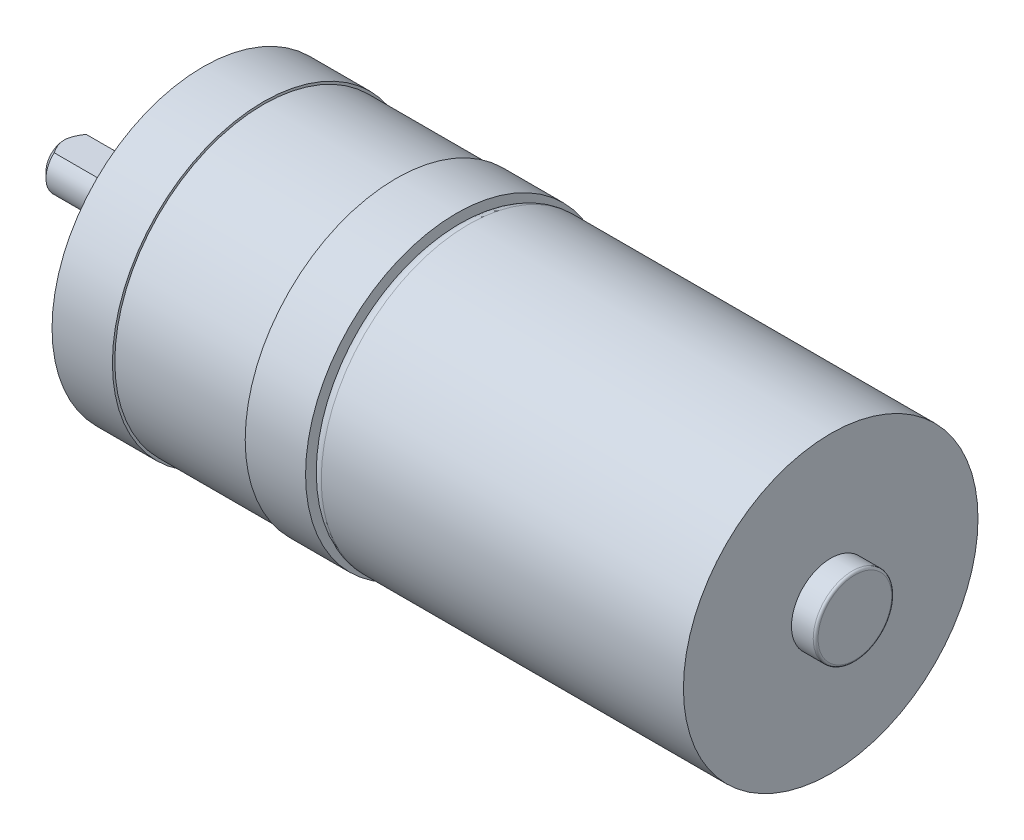
SolidWorks part; units mm, degrees
ref_plane "Front Plane" through (0, 0, 0) normal (0, 0, 1) x (1, 0, 0)
ref_plane "Top Plane" through (0, 0, 0) normal (0, 1, 0) x (1, 0, 0)
ref_plane "Right Plane" through (0, 0, 0) normal (1, 0, 0) x (0, 0, -1)
sketch "Sketch1" plane through (0, 0, 0) normal (0, 0, 1) x (1, 0, 0)
  line L0 (-23.0064, 0) -> (42.0533, 0) construction
  line L1 (-9.9467, -3.5317) -> (-9.9467, -12.5)
  line L2 (-12.4467, -2) -> (-12.4467, -3.5317)
  line L3 (-12.4467, -3.5317) -> (-9.9467, -3.5317)
  line L4 (-21.4467, 0) -> (-21.4467, -1.5)
  line L5 (-12.4467, 0) -> (-12.4467, -12.5) construction
  line L6 (-20.9467, -2) -> (-12.4467, -2)
  line L7 (-23.0064, -2) -> (27.3668, -2) construction
  line L8 (-21.4467, 0) -> (-21.4467, -12.5) construction
  line L9 (-9.9467, 0) -> (-9.9467, -12.5) construction
  line L10 (-21.4467, 0) -> (44.0533, 0)
  line L11 (11.0533, -11.2) -> (11.0533, -12.5)
  line L12 (-9.9467, -12.5) -> (-4.9467, -12.5)
  line L13 (11.0533, -3.5317) -> (11.0533, -12.5) construction
  line L14 (12.0533, -12.2) -> (42.0533, -12.2)
  line L15 (42.0533, -12.2) -> (42.0533, -3.25)
  line L16 (-23.0064, 0) -> (27.3668, 0) construction
  line L17 (-21.4467, -1.5) -> (-20.9467, -2)
  line L18 (-4.9467, -12.3) -> (-4.9467, -12.5)
  line L19 (6.0533, -12.3) -> (6.0533, -12.5)
  line L20 (-4.9467, -12.3) -> (6.0533, -12.3)
  line L21 (-4.9467, -3.5317) -> (-4.9467, -12.5) construction
  line L22 (-9.9467, -12.3) -> (11.0533, -12.3) construction
  line L23 (6.0533, -12.5) -> (11.0533, -12.5)
  line L24 (-9.9467, -12.5) -> (11.0533, -12.5) construction
  line L25 (6.0533, -12.2) -> (6.0533, -12.5) construction
  line L26 (44.0533, -3.05) -> (44.0533, 0)
  line L28 (44.0533, -12.2) -> (44.0533, 0) construction
  line L29 (42.0533, -12.2) -> (42.0533, 0) construction
  line L30 (42.0533, -3.25) -> (43.8533, -3.25)
  line L31 (11.0533, -12.2) -> (11.0533, -12.5) construction
  arc A0 (43.8533, -3.25) -> (44.0533, -3.05) centre (43.8533, -3.05) ccw
  arc A1 (12.0533, -12.2) -> (11.0533, -11.2) centre (12.0533, -11.2) cw
  point P13 (-21.4467, -2)
  dimension "D8" = 0.2
  dimension "D6" = 1
  dimension "D1" = 5
  dimension "D10" = 12.2
  dimension "D11" = 1.8
  dimension "D2" = 2.5
  dimension "D3" = 11.5
  dimension "D4" = 2
  dimension "D5" = 21
  dimension "D7" = 5
revolve "Revolve1" add sketch "Sketch1" angle 360 about L10
sketch "Sketch2" plane through (-21.4467, 0, 0) normal (-1, 0, 0) x (0, 0, 1)
  line L0 (-1.3229, 1.5) -> (1.3229, 1.5)
  arc A0 (1.3229, 1.5) -> (-1.3229, 1.5) centre (0, 0) ccw
extrude "Cut-Extrude1" cut sketch "Sketch2" against normal blind 8
sketch "Sketch3" [suppressed] plane through (42.0533, 0, 0) normal (1, 0, 0) x (0, 0, -1)
  line L0 (-10.5, 0) -> (-9.5, 0) construction
  line L1 (-10.5, -1) -> (-9.5, -1)
  line L2 (-10.5, -1) -> (-10.5, 1)
  line L4 (-10.5, 1) -> (-9.5, 1)
  line L5 (0, 3.05) -> (0, -3.05) construction
  line L6 (10.5, 0) -> (9.5, 0) construction
  line L7 (-12.5, 1) -> (12.5, 1) construction
  line L8 (-12.5, 0) -> (12.5, 0) construction
  line L9 (-12.5, -1) -> (12.5, -1) construction
  line L10 (-9.5, -1) -> (-9.5, 1)
  line L11 (9.5, -1) -> (9.5, 1)
  line L12 (10.5, 1) -> (9.5, 1)
  line L13 (10.5, -1) -> (10.5, 1)
  line L14 (10.5, -1) -> (9.5, -1)
  circle A1 centre (0, 0) radius 3.05 construction
extrude "Boss-Extrude1" [suppressed] add sketch "Sketch3" along normal blind 4
sketch "Sketch4" [suppressed] plane through (0, 0, 10.5) normal (0, 0, 1) x (1, 0, 0)
  line L0 (46.0533, 0.5) -> (46.0533, -0.5)
  line L1 (45.5533, -1) -> (44.0533, -1)
  line L2 (46.0533, -1) -> (42.0533, -1) construction
  line L6 (45.5533, -1) -> (46.0533, -1)
  line L7 (45.5533, 1) -> (46.0533, 0.5)
  line L8 (46.0533, -0.5) -> (45.5533, -1)
  line L9 (45.5533, 1) -> (46.0533, 1)
  line L10 (46.0533, 1) -> (46.0533, 0.5)
  line L11 (45.5533, -1) -> (46.0533, -1)
  line L12 (46.0533, -1) -> (46.0533, -0.5)
  line L13 (46.0533, -1) -> (46.0533, -0.5)
  circle A0 centre (45.0533, 0) radius 0.5031
  point P0 (46.0533, 1)
  line M2 (42.0533, -1) -> (46.0533, -1)
  line M3 (46.0533, -1) -> (46.0533, 1)
  line M4 (46.0533, 1) -> (42.0533, 1)
extrude "Cut-Extrude3" [suppressed] cut sketch "Sketch4" against normal blind 44 contours L8 M3 M2 | L7 M4 M3 | A0
